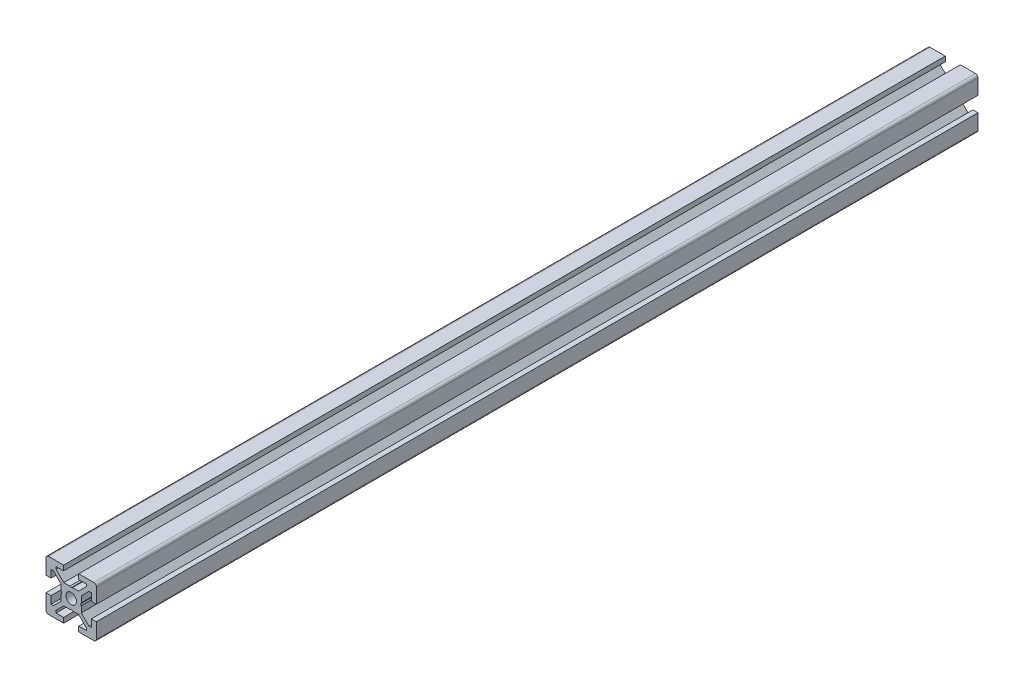
SolidWorks part; units mm, degrees
material "2014 合金"
ref_plane "正面" through (0, 0, 0) normal (0, 0, 1) x (1, 0, 0)
ref_plane "平面" through (0, 0, 0) normal (0, 1, 0) x (1, 0, 0)
ref_plane "右側面" through (0, 0, 0) normal (1, 0, 0) x (0, 0, -1)
ref_plane "平面1" through (0, 0, 0) normal (0, 0, 1) x (1, 0, 0)
sketch "ｽｹｯﾁ1" plane through (0, 0, 0) normal (0, 0, 1) x (1, 0, 0)
  line L0 (-10, -3) -> (-10, -9)
  line L1 (-9, -10) -> (-3, -10)
  line L2 (-3, -10) -> (-3, -8)
  line L3 (-3, -8) -> (-6, -8)
  line L4 (-6, -8) -> (-6, -7.0607)
  line L5 (-6, -7.0607) -> (-2.9393, -4)
  line L6 (-2.9393, -4) -> (-0.5196, -4)
  line L7 (-0.5196, -4) -> (0, -3.7)
  line L8 (0, -3.7) -> (0.5196, -4)
  line L9 (0.5196, -4) -> (2.9393, -4)
  line L10 (2.9393, -4) -> (6, -7.0607)
  line L11 (6, -7.0607) -> (6, -8)
  line L12 (6, -8) -> (3, -8)
  line L13 (3, -8) -> (3, -10)
  line L14 (3, -10) -> (9, -10)
  line L15 (10, -9) -> (10, -3)
  line L16 (10, -3) -> (8, -3)
  line L17 (8, -3) -> (8, -6)
  line L18 (8, -6) -> (7.0607, -6)
  line L19 (7.0607, -6) -> (4, -2.9393)
  line L20 (4, -2.9393) -> (4, -0.5196)
  line L21 (4, -0.5196) -> (3.7, 0)
  line L22 (3.7, 0) -> (4, 0.5196)
  line L23 (4, 0.5196) -> (4, 2.9393)
  line L24 (4, 2.9393) -> (7.0607, 6)
  line L25 (7.0607, 6) -> (8, 6)
  line L26 (8, 6) -> (8, 3)
  line L27 (8, 3) -> (10, 3)
  line L28 (10, 3) -> (10, 9)
  line L29 (9, 10) -> (3, 10)
  line L30 (3, 10) -> (3, 8)
  line L31 (3, 8) -> (6, 8)
  line L32 (6, 8) -> (6, 7.0607)
  line L33 (6, 7.0607) -> (2.9393, 4)
  line L34 (2.9393, 4) -> (0.5196, 4)
  line L35 (0.5196, 4) -> (0, 3.7)
  line L36 (0, 3.7) -> (-0.5196, 4)
  line L37 (-0.5196, 4) -> (-2.9393, 4)
  line L38 (-2.9393, 4) -> (-6, 7.0607)
  line L39 (-6, 7.0607) -> (-6, 8)
  line L40 (-6, 8) -> (-3, 8)
  line L41 (-3, 8) -> (-3, 10)
  line L42 (-3, 10) -> (-9, 10)
  line L43 (-10, 9) -> (-10, 3)
  line L44 (-10, 3) -> (-8, 3)
  line L45 (-8, 3) -> (-8, 6)
  line L46 (-8, 6) -> (-7.0607, 6)
  line L47 (-7.0607, 6) -> (-4, 2.9393)
  line L48 (-4, 2.9393) -> (-4, 0.5196)
  line L49 (-4, 0.5196) -> (-3.7, 0)
  line L50 (-3.7, 0) -> (-4, -0.5196)
  line L51 (-4, -0.5196) -> (-4, -2.9393)
  line L52 (-4, -2.9393) -> (-7.0607, -6)
  line L53 (-7.0607, -6) -> (-8, -6)
  line L54 (-8, -6) -> (-8, -3)
  line L55 (-8, -3) -> (-10, -3)
  arc A0 (-10, -9) -> (-9, -10) centre (-9, -9) ccw
  arc A1 (9, -10) -> (10, -9) centre (9, -9) ccw
  arc A2 (10, 9) -> (9, 10) centre (9, 9) ccw
  arc A3 (-9, 10) -> (-10, 9) centre (-9, 9) ccw
extrude "ﾎﾞｽ - 押し出し1" add sketch "ｽｹｯﾁ1" against normal blind 350
ref_plane "平面2" through (0, 0, 0) normal (1, 0, 0) x (0, 0, -1)
sketch "ｽｹｯﾁ2" plane through (0, 0, 0) normal (1, 0, 0) x (0, 0, -1)
  line L0 (0, 0) -> (0, 2.1)
  line L1 (0, 2.1) -> (260, 2.1)
  line L2 (260, 2.1) -> (260, 0)
  line L3 (260, 0) -> (0, 0)
  line L4 (260, 0) -> (0, 0) construction
revolve "ｶｯﾄ - 回転1" cut sketch "ｽｹｯﾁ2" angle 360 about L4
